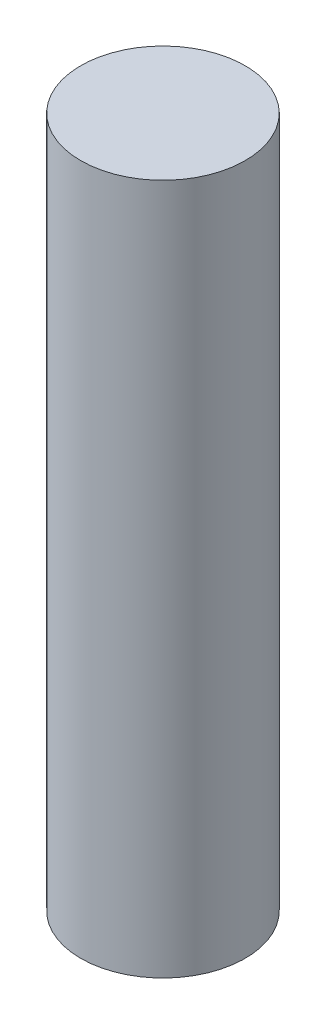
SolidWorks part; units mm, degrees
ref_plane "Front Plane" through (0, 0, 0) normal (0, 0, 1) x (1, 0, 0)
ref_plane "Top Plane" through (0, 0, 0) normal (0, 1, 0) x (1, 0, 0)
ref_plane "Right Plane" through (0, 0, 0) normal (1, 0, 0) x (0, 0, -1)
sketch "Sketch1" plane through (0, 0, 0) normal (0, 1, 0) x (1, 0, 0)
  circle A0 centre (0, 0) radius 7.5
  dimension "D1" = 15
extrude "Boss-Extrude1" add sketch "Sketch1" along normal blind 63
